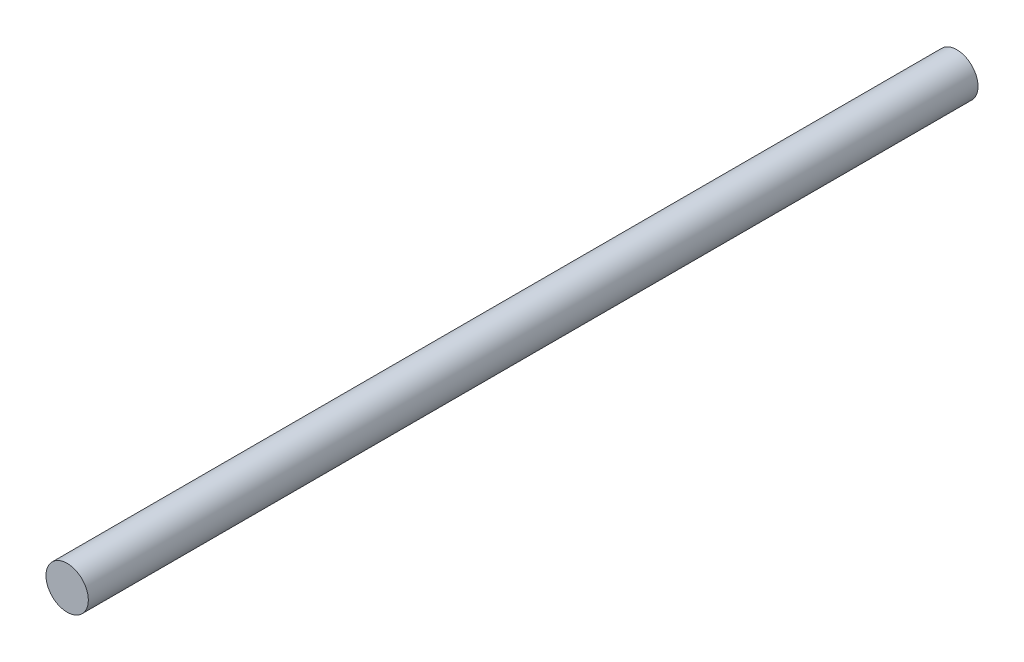
SolidWorks part; units mm, degrees
ref_plane "Front Plane" through (0, 0, 0) normal (0, 0, 1) x (1, 0, 0)
ref_plane "Top Plane" through (0, 0, 0) normal (0, 1, 0) x (1, 0, 0)
ref_plane "Right Plane" through (0, 0, 0) normal (1, 0, 0) x (0, 0, -1)
sketch "Sketch1" plane through (0, 0, 0) normal (0, 0, 1) x (1, 0, 0)
  circle A0 centre (-0.573, -0.8195) radius 1
extrude "Boss-Extrude1" add sketch "Sketch1" along normal blind 42
